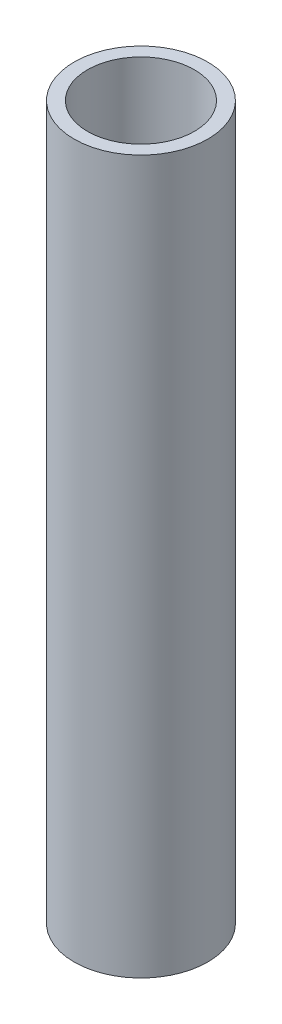
SolidWorks part; units mm, degrees
ref_plane "Front Plane" through (0, 0, 0) normal (0, 0, 1) x (1, 0, 0)
ref_plane "Top Plane" through (0, 0, 0) normal (0, 1, 0) x (1, 0, 0)
ref_plane "Right Plane" through (0, 0, 0) normal (1, 0, 0) x (0, 0, -1)
sketch "Sketch1" plane through (0, 0, 0) normal (0, 1, 0) x (1, 0, 0)
  circle A0 centre (0, 0) radius 4.7625
  circle A1 centre (0, 0) radius 3.81
  dimension "D1" = 9.525
  dimension "D2" = 7.62
extrude "Boss-Extrude1" add sketch "Sketch1" along normal blind 50.8
